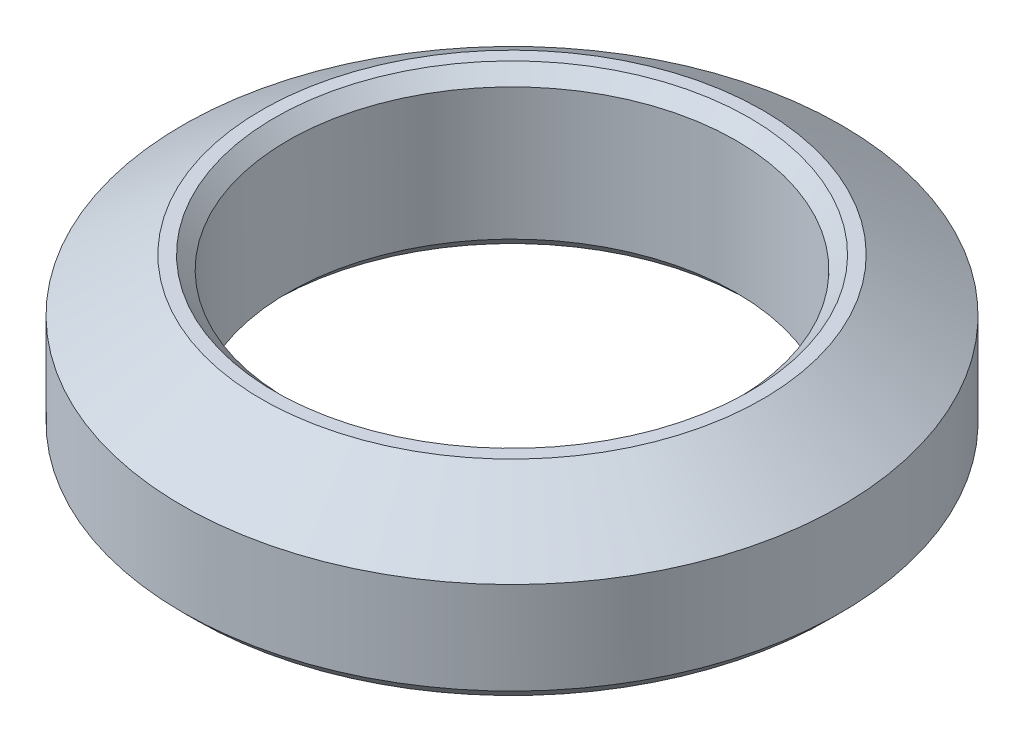
SolidWorks part; units mm, degrees
ref_plane "Front Plane" through (0, 0, 0) normal (0, 0, 1) x (1, 0, 0)
ref_plane "Top Plane" through (0, 0, 0) normal (0, 1, 0) x (1, 0, 0)
ref_plane "Right Plane" through (0, 0, 0) normal (1, 0, 0) x (0, 0, -1)
sketch "Sketch1" plane through (0, 0, 0) normal (0, 0, 1) x (1, 0, 0)
  line L0 (0, 0) -> (0, 3) construction
  line L1 (-4.25, 3) -> (-4.25, 0)
  line L2 (-4.25, 0) -> (-6.25, 0)
  line L3 (-6.25, 0) -> (-6.25, 2)
  line L4 (-6.25, 2) -> (-4.75, 3)
  line L5 (-4.75, 3) -> (-4.25, 3)
  dimension "D1" = 3
  dimension "D2" = 2
  dimension "D3" = 6.25
  dimension "D4" = 4.25
  dimension "D5" = 0.5
revolve "Revolve1" add sketch "Sketch1" angle 360 about L0
chamfer "Chamfer1" distance 0.25 angle 45 3 edges at (0, 3, -4.25) (0, 0, -4.25) (0, 0, -6.25)
